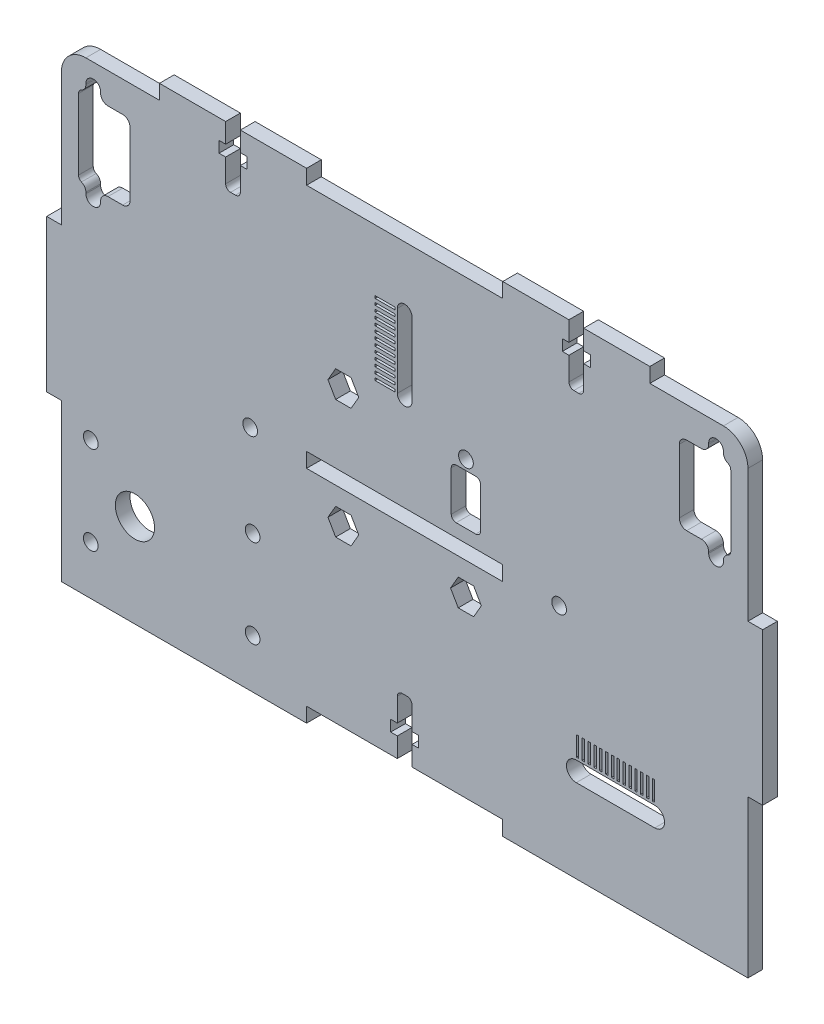
SolidWorks part; units mm, degrees
other "Marcação1"
sketch "Esboço7" plane through (-68, 31.5, 3) normal (-0.6758, 0.2828, 0.6807) x (0.7271, 0.1043, 0.6785)
sketch "Esboço8" plane through (-68, 31.5, 3) normal (-0.6758, 0.2828, 0.6807) x (0.7271, 0.1043, 0.6785)
sketch "Esboço9" plane through (-68, 31.5, 3) normal (-0.6758, 0.2828, 0.6807) x (0.7271, 0.1043, 0.6785)
sketch "Esboço10" plane through (-68, 31.5, 3) normal (-0.6758, 0.2828, 0.6807) x (0.7271, 0.1043, 0.6785)
sketch "Esboço11" plane through (-68, 36.25, 3) normal (-0.6758, 0.2828, 0.6807) x (0.7271, 0.1043, 0.6785)
sketch "Esboço13" plane through (-68, 36.25, 3) normal (-0.6758, 0.2828, 0.6807) x (0.7271, 0.1043, 0.6785)
sketch "Esboço15" plane through (-68, 36.25, 3) normal (-0.6758, 0.2828, 0.6807) x (0.7271, 0.1043, 0.6785)
sketch "Esboço19" plane through (-68, 66.25, 3) normal (-0.6758, 0.2828, 0.6807) x (0.7271, 0.1043, 0.6785)
sketch "Esboço22" plane through (-68, 95.5577, 3) normal (-0.6758, 0.2828, 0.6807) x (0.7271, 0.1043, 0.6785)
material "Acrylic (Medium-high impact)"
ref_plane "Plano frontal" through (0, 0, 0) normal (0, 0, 1) x (1, 0, 0)
ref_plane "Plano superior" through (0, 0, 0) normal (0, 1, 0) x (1, 0, 0)
ref_plane "Plano direito" through (0, 0, 0) normal (1, 0, 0) x (0, 0, -1)
sketch "Esboço1" plane through (0, 0, 0) normal (0, 0, 1) x (1, 0, 0)
  line L6 (70, -47.5) -> (-70, -47.5)
  line L8 (70, -47.5) -> (70, 47.5)
  line L9 (70, 47.5) -> (-70, 47.5)
  line L10 (-70, -47.5) -> (-70, 47.5)
  line L11 (70, -47.5) -> (-70, 47.5) construction
  line L12 (70, 47.5) -> (-70, -47.5) construction
  point P0 (0, 0)
  dimension "D1" = 95
  dimension "D2" = 140
extrude "Ressalto-extrusão1" add sketch "Esboço1" along normal mid plane 3
sketch "Esboço2" plane through (0, 0, 1.5) normal (0, 0, 1) x (1, 0, 0)
  line L1 (-20, -47.5) -> (20, -47.5)
  line L2 (-20, -47.5) -> (-20, -44.5)
  line L3 (-20, -44.5) -> (20, -44.5)
  line L4 (20, -47.5) -> (20, -44.5)
  line L6 (-70, -47.5) -> (70, -47.5) construction
  line L21 (-20, 0.5) -> (20, 0.5)
  line L22 (-20, 0.5) -> (-20, -2.5)
  line L23 (-20, -2.5) -> (20, -2.5)
  line L24 (20, 0.5) -> (20, -2.5)
  line L25 (-20, 0.5) -> (20, -2.5) construction
  line L26 (-20, -2.5) -> (20, 0.5) construction
  line L28 (0, -1.65) -> (0, 1.65) construction
  circle A2 centre (-31.5, -1) radius 1.5
  circle A4 centre (31.5, -1) radius 1.5
  point P6 (0, -44.5)
  point P14 (0, -1)
  point P29 (-20, -1)
  dimension "D4" = 3
  dimension "D8" = 3
  dimension "D9" = 10
  dimension "D2" = 40
  dimension "D3" = 45
  dimension "D6" = 3
  dimension "D13" = 40
extrude "Corte-extrusão1" cut sketch "Esboço2" against normal through all
sketch "Esboço3" plane through (0, 0, 1.5) normal (0, 0, 1) x (1, 0, 0)
  line L0 (70, -47.5) -> (70, 47.5) construction
  line L1 (70, 15.5) -> (73, 15.5)
  line L2 (70, 15.5) -> (70, -15.5)
  line L3 (70, -15.5) -> (73, -15.5)
  line L4 (73, 15.5) -> (73, -15.5)
  line L5 (0, -1.65) -> (0, 1.65) construction
  line L6 (-70, -15.5) -> (-73, -15.5)
  line L7 (-70, 15.5) -> (-73, 15.5)
  line L8 (-70, 15.5) -> (-70, -15.5)
  line L9 (-73, 15.5) -> (-73, -15.5)
  line L10 (70, 47.5) -> (-70, 47.5) construction
  line L11 (-50, 50.5) -> (-20, 50.5)
  line L12 (-50, 50.5) -> (-50, 47.5)
  line L13 (-50, 47.5) -> (-20, 47.5)
  line L14 (-20, 50.5) -> (-20, 47.5)
  line L15 (20, 50.5) -> (20, 47.5)
  line L16 (50, 47.5) -> (20, 47.5)
  line L17 (50, 50.5) -> (50, 47.5)
  line L18 (50, 50.5) -> (20, 50.5)
  line L19 (0, -37.5) -> (0, 37.5) construction
  line L20 (-70, 47.5) -> (-70, -47.5) construction
  point P6 (70, 0)
  point P28 (0, 0)
  dimension "D1" = 3
  dimension "D2" = 31
  dimension "D3" = 3
  dimension "D4" = 30
  dimension "D5" = 20
  dimension "D6" = 20
extrude "Ressalto-extrusão2" add sketch "Esboço3" against normal through all
sketch "Esboço30" plane through (0, 0, -1.5) normal (0, 0, -1) x (-1, 0, 0)
  line L0 (73, 15.5) -> (73, -15.5) construction
  line L1 (70, -47.5) -> (20, -47.5) construction
  circle A0 centre (55, -28.5) radius 4
  dimension "D1" = 8
  dimension "D2" = 18
  dimension "D3" = 19
extrude "Corte-extrusão11" cut sketch "Esboço30" against normal through all both and the other way through all
sketch "Esboço31" plane through (0, 0, -1.5) normal (0, 0, -1) x (-1, 0, 0)
  circle A4 centre (64, -19.5) radius 1.5
  circle A5 centre (64, -37.5) radius 1.5
  circle A6 centre (55, -28.5) radius 4 construction
  circle A7 centre (31, -19.5) radius 1.5
  circle A8 centre (31, -37.5) radius 1.5
  dimension "D1" = 3
  dimension "D2" = 9
  dimension "D3" = 9
  dimension "D4" = 18
  dimension "D5" = 33
extrude "Corte-extrusão12" cut sketch "Esboço31" against normal through all both and the other way through all
sketch "Esboço4" plane through (0, 0, 1.5) normal (0, 0, 1) x (1, 0, 0)
  line L0 (-59, -28.5) -> (-51, -28.5) construction
  line L1 (35, -28.5) -> (51, -28.5) construction
  line L2 (35, -26.5) -> (51, -26.5)
  line L3 (35, -30.5) -> (51, -30.5)
  line L5 (35, -22) -> (35.5, -22)
  line L6 (35, -22) -> (35, -26)
  line L7 (35, -26) -> (35.5, -26)
  line L8 (35.5, -22) -> (35.5, -26)
  line L9 (36.1923, -22) -> (36.6923, -22)
  line L10 (36.1923, -22) -> (36.1923, -26)
  line L11 (36.1923, -26) -> (36.6923, -26)
  line L12 (36.6923, -22) -> (36.6923, -26)
  line L13 (37.3846, -22) -> (37.8846, -22)
  line L14 (37.3846, -22) -> (37.3846, -26)
  line L15 (37.3846, -26) -> (37.8846, -26)
  line L16 (37.8846, -22) -> (37.8846, -26)
  line L17 (38.5769, -22) -> (39.0769, -22)
  line L18 (38.5769, -22) -> (38.5769, -26)
  line L19 (38.5769, -26) -> (39.0769, -26)
  line L20 (39.0769, -22) -> (39.0769, -26)
  line L21 (39.7692, -22) -> (40.2692, -22)
  line L22 (39.7692, -22) -> (39.7692, -26)
  line L23 (39.7692, -26) -> (40.2692, -26)
  line L24 (40.2692, -22) -> (40.2692, -26)
  line L25 (40.9615, -22) -> (41.4615, -22)
  line L26 (40.9615, -22) -> (40.9615, -26)
  line L27 (40.9615, -26) -> (41.4615, -26)
  line L28 (41.4615, -22) -> (41.4615, -26)
  line L29 (42.1538, -22) -> (42.6538, -22)
  line L30 (42.1538, -22) -> (42.1538, -26)
  line L31 (42.1538, -26) -> (42.6538, -26)
  line L32 (42.6538, -22) -> (42.6538, -26)
  line L33 (43.3462, -22) -> (43.8462, -22)
  line L34 (43.3462, -22) -> (43.3462, -26)
  line L35 (43.3462, -26) -> (43.8462, -26)
  line L36 (43.8462, -22) -> (43.8462, -26)
  line L37 (44.5385, -22) -> (45.0385, -22)
  line L38 (44.5385, -22) -> (44.5385, -26)
  line L39 (44.5385, -26) -> (45.0385, -26)
  line L40 (45.0385, -22) -> (45.0385, -26)
  line L41 (45.7308, -22) -> (46.2308, -22)
  line L42 (45.7308, -22) -> (45.7308, -26)
  line L43 (45.7308, -26) -> (46.2308, -26)
  line L44 (46.2308, -22) -> (46.2308, -26)
  line L45 (46.9231, -22) -> (47.4231, -22)
  line L46 (46.9231, -22) -> (46.9231, -26)
  line L47 (46.9231, -26) -> (47.4231, -26)
  line L48 (47.4231, -22) -> (47.4231, -26)
  line L49 (48.1154, -22) -> (48.6154, -22)
  line L50 (48.1154, -22) -> (48.1154, -26)
  line L51 (48.1154, -26) -> (48.6154, -26)
  line L52 (48.6154, -22) -> (48.6154, -26)
  line L53 (49.3077, -22) -> (49.8077, -22)
  line L54 (49.3077, -22) -> (49.3077, -26)
  line L55 (49.3077, -26) -> (49.8077, -26)
  line L56 (49.8077, -22) -> (49.8077, -26)
  line L57 (50.5, -22) -> (51, -22)
  line L58 (50.5, -22) -> (50.5, -26)
  line L59 (50.5, -26) -> (51, -26)
  line L60 (51, -22) -> (51, -26)
  circle A9 centre (-55, -28.5) radius 4 construction
  circle A10 centre (43, -28.5) radius 2 construction
  arc A11 (35, -26.5) -> (35, -30.5) centre (35, -28.5) ccw
  arc A12 (51, -30.5) -> (51, -26.5) centre (51, -28.5) ccw
  point P9 (43, -28.5)
  dimension "D1" = 98
  dimension "D4" = 0.5
  dimension "D2" = 4
  dimension "D3" = 8
  dimension "D5" = 4
  dimension "D6" = 0.5
  dimension "D7" = 14
extrude "Corte-extrusão2" cut sketch "Esboço4" against normal through all
sketch "Sketch5" plane through (0, 0, 0) normal (0, 0, 1) x (1, 0, 0)
  line L0 (20, -44.5) -> (-20, -44.5) construction
  line L1 (-1.5, -44.5) -> (1.5, -44.5)
  line L2 (-1.5, -44.5) -> (-1.5, -40.5)
  line L3 (-0.5, -32.5) -> (0.5, -32.5)
  line L4 (1.5, -44.5) -> (1.5, -40.5)
  line L5 (1.5, -38.23) -> (2.85, -38.23)
  line L6 (-2.85, -38.23) -> (-1.5, -38.23)
  line L7 (-2.85, -38.23) -> (-2.85, -40.5)
  line L8 (-2.85, -40.5) -> (-1.5, -40.5)
  line L9 (2.85, -38.23) -> (2.85, -40.5)
  line L10 (-1.5, -38.23) -> (-1.5, -33.5)
  line L11 (1.5, -40.5) -> (2.85, -40.5)
  line L12 (1.5, -38.23) -> (1.5, -33.5)
  arc A0 (0.5, -32.5) -> (1.5, -33.5) centre (0.5, -33.5) cw
  arc A1 (-1.5, -33.5) -> (-0.5, -32.5) centre (-0.5, -33.5) cw
  point P6 (0, -32.5)
  point P18 (1.5, -32.5)
  point P21 (-1.5, -32.5)
  dimension "D7" = 1
  dimension "D1" = 12
  dimension "D2" = 3
  dimension "D3" = 2.27
  dimension "D4" = 1.35
  dimension "D5" = 1.35
  dimension "D6" = 4
extrude "Cut-Extrude2" cut sketch "Sketch5" against normal through all both and the other way through all
sketch "Sketch8" plane through (0, 0, 1.5) normal (0, 0, 1) x (1, 0, 0)
  line L12 (0, -1.65) -> (0, 1.65) construction
  line L13 (-70, 47.5) -> (-70, 15.5) construction
  line L14 (70, 47.5) -> (50, 47.5) construction
  line B0 (-70, 33.25) -> (-56, 33.25) construction
  line B1 (-68.5, 41.25) -> (-66.5, 41.25) construction
  line B2 (-70, 39.75) -> (-70, 26.75) construction
  line B3 (-68.5, 25.25) -> (-66.5, 25.25) construction
  line B4 (-56, 39.75) -> (-56, 26.75)
  line B5 (-65, 23.5) -> (-65, 23.75)
  line B6 (-62, 23.5) -> (-62, 23.75)
  line B7 (-60.5, 25.25) -> (-57.5, 25.25)
  line B8 (-65, 43) -> (-65, 42.75)
  line B9 (-62, 43) -> (-62, 42.75)
  line B10 (-60.5, 41.25) -> (-57.5, 41.25)
  line B11 (-66.5, 40.4587) -> (-66.5, 26.0413)
  arc B12 (-62, 43) -> (-65, 43) centre (-63.5, 43) ccw
  arc B13 (-65, 23.5) -> (-62, 23.5) centre (-63.5, 23.5) ccw
  arc B14 (-62, 23.75) -> (-60.5, 25.25) centre (-60.5, 23.75) cw
  arc B15 (-65, 23.75) -> (-65.9, 25.1248) centre (-66.5, 23.75) ccw
  arc B16 (-62, 42.75) -> (-60.5, 41.25) centre (-60.5, 42.75) ccw
  arc B17 (-65, 42.75) -> (-65.9, 41.3752) centre (-66.5, 42.75) cw
  arc B18 (-70, 26.75) -> (-68.5, 25.25) centre (-68.5, 26.75) ccw construction
  arc B19 (-57.5, 25.25) -> (-56, 26.75) centre (-57.5, 26.75) ccw
  arc B20 (-57.5, 41.25) -> (-56, 39.75) centre (-57.5, 39.75) cw
  arc B21 (-68.5, 41.25) -> (-70, 39.75) centre (-68.5, 39.75) ccw construction
  arc B22 (-66.5, 26.0413) -> (-65.9, 25.1248) centre (-65.5, 26.0413) ccw
  arc B23 (-66.5, 40.4587) -> (-65.9, 41.3752) centre (-65.5, 40.4587) cw
  line B24 (56, 39.75) -> (56, 26.75)
  line B25 (65, 23.5) -> (65, 23.75)
  line B26 (62, 23.5) -> (62, 23.75)
  line B27 (60.5, 25.25) -> (57.5, 25.25)
  line B28 (65, 43) -> (65, 42.75)
  line B29 (62, 43) -> (62, 42.75)
  line B30 (60.5, 41.25) -> (57.5, 41.25)
  line B31 (66.5, 40.4587) -> (66.5, 26.0413)
  arc B32 (62, 43) -> (65, 43) centre (63.5, 43) cw
  arc B33 (65, 23.5) -> (62, 23.5) centre (63.5, 23.5) cw
  arc B34 (62, 23.75) -> (60.5, 25.25) centre (60.5, 23.75) ccw
  arc B35 (65, 23.75) -> (65.9, 25.1248) centre (66.5, 23.75) cw
  arc B36 (62, 42.75) -> (60.5, 41.25) centre (60.5, 42.75) cw
  arc B37 (65, 42.75) -> (65.9, 41.3752) centre (66.5, 42.75) ccw
  arc B38 (57.5, 25.25) -> (56, 26.75) centre (57.5, 26.75) cw
  arc B39 (57.5, 41.25) -> (56, 39.75) centre (57.5, 39.75) ccw
  arc B40 (66.5, 26.0413) -> (65.9, 25.1248) centre (65.5, 26.0413) cw
  arc B41 (66.5, 40.4587) -> (65.9, 41.3752) centre (65.5, 40.4587) ccw
  dimension "D1" = 3
sketch_block_instance "Block6-1"
sketch_block "Block6" parameters "D1"=3, "D2"=1.5, "D3"=1.5, "D5"=1, "D4"=5, "D6"=12
sketch_block_instance "Block6-2"
extrude "Cut-Extrude6" cut sketch "Sketch8" against normal through all both and the other way through all
sketch "Sketch11" plane through (0, 0, 0) normal (0, 0, 1) x (1, 0, 0)
  line L0 (-20, 50.5) -> (-50, 50.5) construction
  line L1 (-36.5, 50.5) -> (-33.5, 50.5)
  line L2 (-36.5, 50.5) -> (-36.5, 46.5)
  line L3 (-35.5, 38.5) -> (-34.5, 38.5)
  line L4 (-33.5, 50.5) -> (-33.5, 46.5)
  line L5 (-50, 50.5) -> (-50, 47.5) construction
  line L6 (-33.5, 46.5) -> (-32.15, 46.5)
  line L7 (-37.85, 46.5) -> (-36.5, 46.5)
  line L8 (-37.85, 46.5) -> (-37.85, 44.23)
  line L9 (-37.85, 44.23) -> (-36.5, 44.23)
  line L10 (-32.15, 46.5) -> (-32.15, 44.23)
  line L11 (-36.5, 44.23) -> (-36.5, 39.5)
  line L12 (-33.5, 44.23) -> (-33.5, 39.5)
  line L13 (-33.5, 44.23) -> (-32.15, 44.23)
  line L14 (0, -1.65) -> (0, 1.65) construction
  line L15 (33.5, 44.23) -> (32.15, 44.23)
  line L16 (33.5, 44.23) -> (33.5, 39.5)
  line L17 (36.5, 44.23) -> (36.5, 39.5)
  line L18 (32.15, 46.5) -> (32.15, 44.23)
  line L19 (37.85, 44.23) -> (36.5, 44.23)
  line L20 (37.85, 46.5) -> (37.85, 44.23)
  line L21 (37.85, 46.5) -> (36.5, 46.5)
  line L22 (33.5, 46.5) -> (32.15, 46.5)
  line L23 (33.5, 50.5) -> (33.5, 46.5)
  line L24 (35.5, 38.5) -> (34.5, 38.5)
  line L25 (36.5, 50.5) -> (36.5, 46.5)
  line L26 (36.5, 50.5) -> (33.5, 50.5)
  arc A0 (-34.5, 38.5) -> (-33.5, 39.5) centre (-34.5, 39.5) ccw
  arc A1 (-36.5, 39.5) -> (-35.5, 38.5) centre (-35.5, 39.5) ccw
  arc A2 (36.5, 39.5) -> (35.5, 38.5) centre (35.5, 39.5) cw
  arc A3 (34.5, 38.5) -> (33.5, 39.5) centre (34.5, 39.5) cw
  point P12 (-36.5, 38.5)
  point P39 (36.5, 38.5)
  dimension "D4" = 1
  dimension "D1" = 3
  dimension "D2" = 12
  dimension "D3" = 13.5
  dimension "D5" = 4
  dimension "D6" = 2.27
  dimension "D7" = 1.35
  dimension "D8" = 1.35
extrude "Cut-Extrude8" cut sketch "Sketch11" against normal through all both and the other way through all
sketch "Sketch12" plane through (0, 0, 1.5) normal (0, 0, 1) x (1, 0, 0)
  line L0 (0, 0.5) -> (0, 47.5) construction
  line L1 (20, 0.5) -> (-20, 0.5) construction
  line L2 (-6, 21.7083) -> (-2, 21.7083)
  line L3 (20, 47.5) -> (-20, 47.5) construction
  line L4 (0, 20) -> (0, 35) construction
  line L7 (-1.5, 20) -> (-1.5, 35)
  line L8 (1.5, 20) -> (1.5, 35)
  line L9 (-6, 20.5) -> (-2, 20.5)
  line L10 (-6, 20.5) -> (-6, 20)
  line L11 (-6, 20) -> (-2, 20)
  line L12 (-2, 20.5) -> (-2, 20)
  line L13 (-6, 21.7083) -> (-6, 21.2083)
  line L14 (-6, 21.2083) -> (-2, 21.2083)
  line L15 (-2, 21.7083) -> (-2, 21.2083)
  line L16 (-6, 22.9167) -> (-2, 22.9167)
  line L17 (-6, 22.9167) -> (-6, 22.4167)
  line L18 (-6, 22.4167) -> (-2, 22.4167)
  line L19 (-2, 22.9167) -> (-2, 22.4167)
  line L20 (-6, 24.125) -> (-2, 24.125)
  line L21 (-6, 24.125) -> (-6, 23.625)
  line L22 (-6, 23.625) -> (-2, 23.625)
  line L23 (-2, 24.125) -> (-2, 23.625)
  line L24 (-6, 25.3333) -> (-2, 25.3333)
  line L25 (-6, 25.3333) -> (-6, 24.8333)
  line L26 (-6, 24.8333) -> (-2, 24.8333)
  line L27 (-2, 25.3333) -> (-2, 24.8333)
  line L28 (-6, 26.5417) -> (-2, 26.5417)
  line L29 (-6, 26.5417) -> (-6, 26.0417)
  line L30 (-6, 26.0417) -> (-2, 26.0417)
  line L31 (-2, 26.5417) -> (-2, 26.0417)
  line L32 (-6, 27.75) -> (-2, 27.75)
  line L33 (-6, 27.75) -> (-6, 27.25)
  line L34 (-6, 27.25) -> (-2, 27.25)
  line L35 (-2, 27.75) -> (-2, 27.25)
  line L36 (-6, 28.9583) -> (-2, 28.9583)
  line L37 (-6, 28.9583) -> (-6, 28.4583)
  line L38 (-6, 28.4583) -> (-2, 28.4583)
  line L39 (-2, 28.9583) -> (-2, 28.4583)
  line L40 (-6, 30.1667) -> (-2, 30.1667)
  line L41 (-6, 30.1667) -> (-6, 29.6667)
  line L42 (-6, 29.6667) -> (-2, 29.6667)
  line L43 (-2, 30.1667) -> (-2, 29.6667)
  line L44 (-6, 31.375) -> (-2, 31.375)
  line L45 (-6, 31.375) -> (-6, 30.875)
  line L46 (-6, 30.875) -> (-2, 30.875)
  line L47 (-2, 31.375) -> (-2, 30.875)
  line L48 (-6, 32.5833) -> (-2, 32.5833)
  line L49 (-6, 32.5833) -> (-6, 32.0833)
  line L50 (-6, 32.0833) -> (-2, 32.0833)
  line L51 (-2, 32.5833) -> (-2, 32.0833)
  line L52 (-6, 33.7917) -> (-2, 33.7917)
  line L53 (-6, 33.7917) -> (-6, 33.2917)
  line L54 (-6, 33.2917) -> (-2, 33.2917)
  line L55 (-2, 33.7917) -> (-2, 33.2917)
  line L56 (-6, 35) -> (-2, 35)
  line L57 (-6, 35) -> (-6, 34.5)
  line L58 (-6, 34.5) -> (-2, 34.5)
  line L59 (-2, 35) -> (-2, 34.5)
  circle A1 centre (0, 20) radius 1.5 construction
  arc A4 (-1.5, 20) -> (1.5, 20) centre (0, 20) ccw
  arc A5 (1.5, 35) -> (-1.5, 35) centre (0, 35) ccw
  point P6 (0, 27.5)
  dimension "D1" = 3
  dimension "D2" = 15
  dimension "D3" = 18
  dimension "D4" = 0.5
  dimension "D5" = 4
  dimension "D6" = 0.5
  dimension "D7" = 13
extrude "Cut-Extrude9" cut sketch "Sketch12" against normal through all
sketch "Sketch16" plane through (0, 0, 0) normal (0, 0, 1) x (1, 0, 0)
  line L0 (-20, -2.5) -> (20, -2.5) construction
  line L1 (20, 0.5) -> (-20, 0.5) construction
  line L2 (-20, 0.5) -> (-20, -2.5) construction
  line L3 (15.64, -8.95) -> (14.07, -6.2307)
  line L4 (10.5, 13.35) -> (14.5, 13.35)
  line L5 (9.5, 12.35) -> (9.5, 4.15)
  line L6 (10.5, 3.15) -> (14.5, 3.15)
  line L7 (15.5, 12.35) -> (15.5, 4.15)
  line L8 (14.07, -6.2307) -> (10.93, -6.2307)
  line L9 (10.93, -6.2307) -> (9.36, -8.95)
  line L10 (9.36, -8.95) -> (10.93, -11.6693)
  line L11 (10.93, -11.6693) -> (14.07, -11.6693)
  line L12 (14.07, -11.6693) -> (15.64, -8.95)
  line L14 (-9.36, 15.35) -> (-10.93, 18.0693)
  line L15 (-10.93, 18.0693) -> (-14.07, 18.0693)
  line L16 (-14.07, 18.0693) -> (-15.64, 15.35)
  line L17 (-15.64, 15.35) -> (-14.07, 12.6307)
  line L18 (-14.07, 12.6307) -> (-10.93, 12.6307)
  line L19 (-10.93, 12.6307) -> (-9.36, 15.35)
  line L20 (-9.36, -8.95) -> (-10.93, -6.2307)
  line L21 (-10.93, -6.2307) -> (-14.07, -6.2307)
  line L22 (-14.07, -6.2307) -> (-15.64, -8.95)
  line L23 (-15.64, -8.95) -> (-14.07, -11.6693)
  line L24 (-14.07, -11.6693) -> (-10.93, -11.6693)
  line L25 (-10.93, -11.6693) -> (-9.36, -8.95)
  circle A0 centre (-12.5, 15.35) radius 1.5 construction
  circle A1 centre (12.5, 15.35) radius 1.5
  circle A2 centre (-12.5, -8.95) radius 1.5 construction
  circle A3 centre (12.5, -8.95) radius 1.5 construction
  arc A4 (9.5, 4.15) -> (10.5, 3.15) centre (10.5, 4.15) ccw
  arc A5 (14.5, 3.15) -> (15.5, 4.15) centre (14.5, 4.15) ccw
  arc A6 (14.5, 13.35) -> (15.5, 12.35) centre (14.5, 12.35) cw
  arc A7 (10.5, 13.35) -> (9.5, 12.35) centre (10.5, 12.35) ccw
  circle A8 centre (12.5, -8.95) radius 2.7193 construction
  circle A9 centre (-12.5, 15.35) radius 2.7193 construction
  circle A10 centre (-12.5, -8.95) radius 2.7193 construction
  point P8 (12.5, 13.35)
  point P21 (15.5, 3.15)
  point P24 (15.5, 13.35)
  dimension "D1" = 3
  dimension "D2" = 25
  dimension "D3" = 24.3
  dimension "D4" = 13.35
  dimension "D5" = 7.5
  dimension "D7" = 1.5
  dimension "D9" = 1
  dimension "D6" = 0.5
  dimension "D8" = 10.2
  dimension "D10" = 3.14
  dimension "D11" = 3.14
  dimension "D12" = 3.14
extrude "Cut-Extrude12" cut sketch "Sketch16" against normal through all both and the other way through all
fillet "Fillet1" radius 5 2 edges at (-70, 47.5, 0) (70, 47.5, 0)
